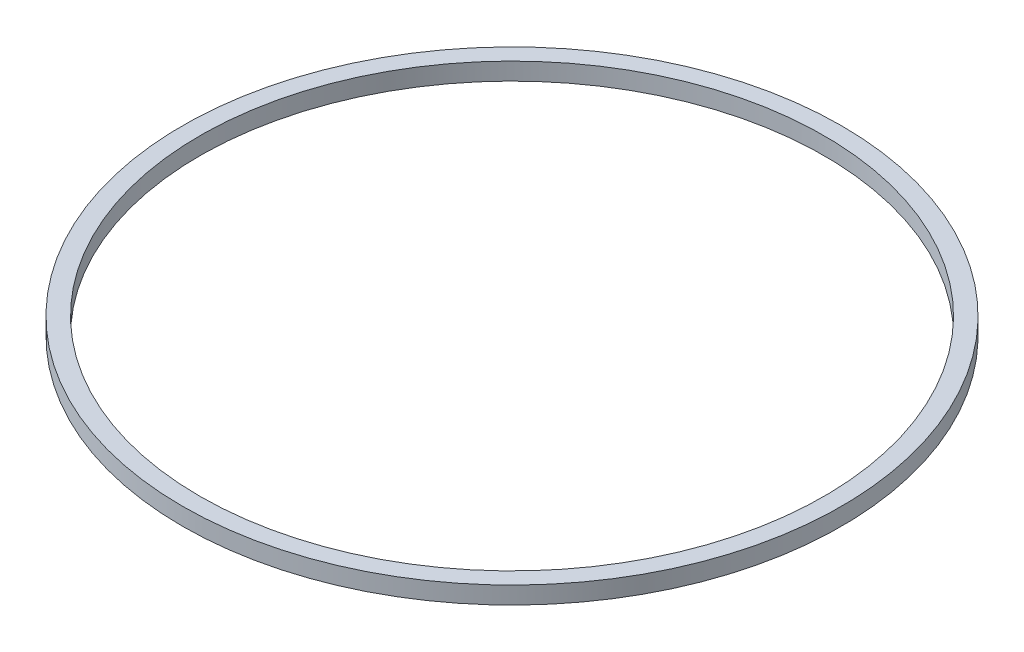
SolidWorks part; units mm, degrees
material "Silicon Rubber"
ref_plane "Front Plane" through (0, 0, 0) normal (0, 0, 1) x (1, 0, 0)
ref_plane "Top Plane" through (0, 0, 0) normal (0, 1, 0) x (1, 0, 0)
ref_plane "Right Plane" through (0, 0, 0) normal (1, 0, 0) x (0, 0, -1)
sketch "Sketch1" plane through (0, 0, 0) normal (0, 1, 0) x (1, 0, 0)
  circle A0 centre (0, 0) radius 54
  circle A1 centre (0, 0) radius 57
  dimension "D1" = 114
  dimension "D2" = 108
extrude "Boss-Extrude1" add sketch "Sketch1" along normal blind 3
